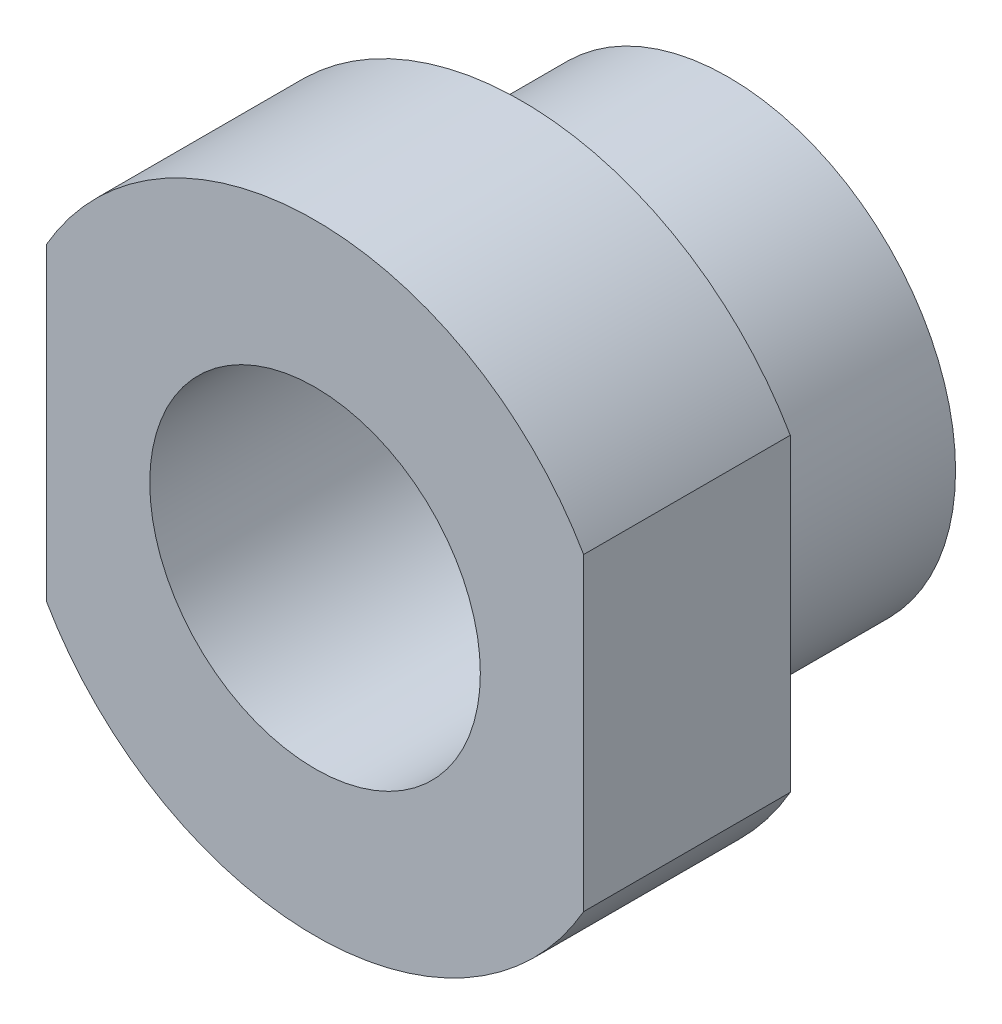
SolidWorks part; units mm, degrees
material "6063-T6"
ref_plane "Front" through (0, 0, 0) normal (0, 0, 1) x (1, 0, 0)
ref_plane "Top" through (0, 0, 0) normal (0, 1, 0) x (1, 0, 0)
ref_plane "Right" through (0, 0, 0) normal (1, 0, 0) x (0, 0, -1)
sketch "Sketch1" plane through (0, 0, 0) normal (0, 0, 1) x (1, 0, 0)
  line L0 (-6.5, 3.7417) -> (-6.5, -3.7417)
  line L1 (0, 12.3353) -> (0, -11.1196) construction
  line L2 (6.5, 3.7417) -> (6.5, -3.7417)
  circle A0 centre (0, 0) radius 4
  arc A1 (-6.5, -3.7417) -> (6.5, -3.7417) centre (0, 0) ccw
  arc A2 (6.5, 3.7417) -> (-6.5, 3.7417) centre (0, 0) ccw
  dimension "D1" = 8
  dimension "D2" = 15
  dimension "D3" = 13
extrude "Boss-Extrude1" add sketch "Sketch1" along normal blind 5
sketch "Sketch2" plane through (0, 0, 0) normal (0, 0, -1) x (-1, 0, 0)
  circle A0 centre (0, 0) radius 5.5
  circle A1 centre (0, 0) radius 4
  dimension "D1" = 11
  dimension "D2" = 8
extrude "Boss-Extrude2" add sketch "Sketch2" along normal blind 5
